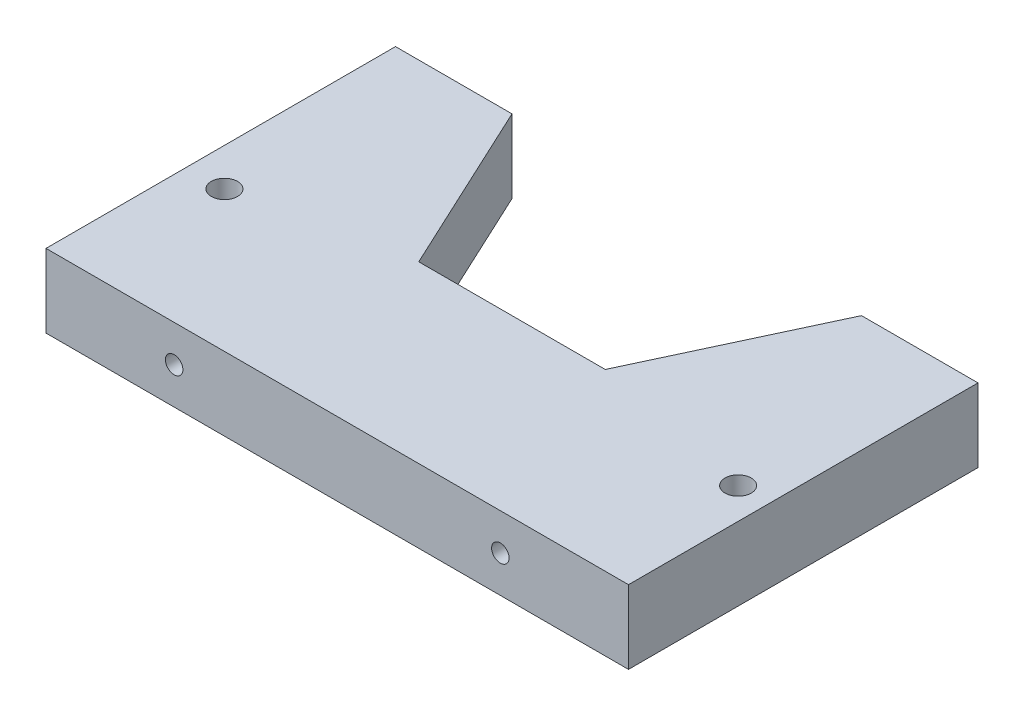
SolidWorks part; units mm, degrees
ref_plane "Front Plane" through (0, 0, 0) normal (0, 0, 1) x (1, 0, 0)
ref_plane "Top Plane" through (0, 0, 0) normal (0, 1, 0) x (1, 0, 0)
ref_plane "Right Plane" through (0, 0, 0) normal (1, 0, 0) x (0, 0, -1)
sketch "Sketch1" plane through (0, 0, 0) normal (0, 1, 0) x (1, 0, 0)
  line L0 (-30, 30) -> (-16.0081, 0)
  line L1 (-50, 30) -> (-30, 30)
  line L2 (-50, 30) -> (-50, -30)
  line L3 (-50, -30) -> (50, -30)
  line L4 (50, 30) -> (50, -30)
  line L5 (-50, 30) -> (50, -30) construction
  line L6 (-50, -30) -> (50, 30) construction
  line L7 (-16.0081, 0) -> (16.0081, 0)
  line L8 (16.0081, 0) -> (30, 30)
  line L9 (30, 30) -> (50, 30)
  point P0 (0, 0)
  point P9 (0, 0)
  dimension "D1" = 100
  dimension "D2" = 60
  dimension "D3" = 20
  dimension "D4" = 20
extrude "Boss-Extrude1" add sketch "Sketch1" along normal blind 12.6
sketch "Sketch2" plane through (0, 0, 30) normal (0, 0, 1) x (1, 0, 0)
  line L0 (-50, 6.3) -> (50, 6.3) construction
  line L1 (-50, 12.6) -> (-50, 0) construction
  line L2 (50, 12.6) -> (50, 0) construction
  circle A0 centre (-28, 6.3) radius 1.5
  circle A1 centre (28, 6.3) radius 1.5
  dimension "D3" = 3
  dimension "D4" = 3
  dimension "D1" = 22
  dimension "D2" = 22
extrude "Cut-Extrude1" cut sketch "Sketch2" against normal blind 20
sketch "Sketch3" plane through (0, 0, 0) normal (0, -1, 0) x (1, 0, 0)
  line L0 (41.6388, 5.8511) -> (-40.9612, 5.8511) construction
  arc A0 (43.8888, 8.1011) -> (43.8888, 3.6011) centre (43.8888, 5.8511) ccw construction
  arc A1 (-43.2112, 3.6011) -> (-43.2112, 8.1011) centre (-43.2112, 5.8511) ccw construction
  circle A2 centre (44.6718, 5.8511) radius 2.25
  circle A3 centre (-43.5196, 5.8511) radius 2.25
  dimension "D1" = 4.5
  dimension "D2" = 4.5
extrude "Cut-Extrude2" cut sketch "Sketch3" against normal up to next
sketch "Sketch4" plane through (0, 0, 0) normal (0, 1, 0) x (1, 0, 0)
  line L8 (50, -30) -> (50, 30)
  line L9 (50, 30) -> (30, 30)
  line L10 (30, 30) -> (16.0081, 0)
  line L11 (16.0081, 0) -> (-16.0081, 0)
  line L12 (-16.0081, 0) -> (-30, 30)
  line L13 (-30, 30) -> (-50, 30)
  line L14 (-50, 30) -> (-50, -30)
  line L15 (-50, -30) -> (50, -30)
  line L16 (50, -30) -> (50, 30)
  line L17 (50, 30) -> (30, 30)
  line L18 (30, 30) -> (16.0081, 0)
  line L19 (16.0081, 0) -> (-16.0081, 0)
  line L20 (-16.0081, 0) -> (-30, 30)
  line L21 (-30, 30) -> (-50, 30)
  line L22 (-50, 30) -> (-50, -30)
  line L23 (-50, -30) -> (50, -30)
  circle A0 centre (-43.5196, -5.8511) radius 2.25 construction
  circle A1 centre (44.6718, -5.8511) radius 2.25 construction
  circle A2 centre (-43.5196, -5.8511) radius 2.25
  circle A3 centre (44.6718, -5.8511) radius 2.25
  dimension "D1" = 0
